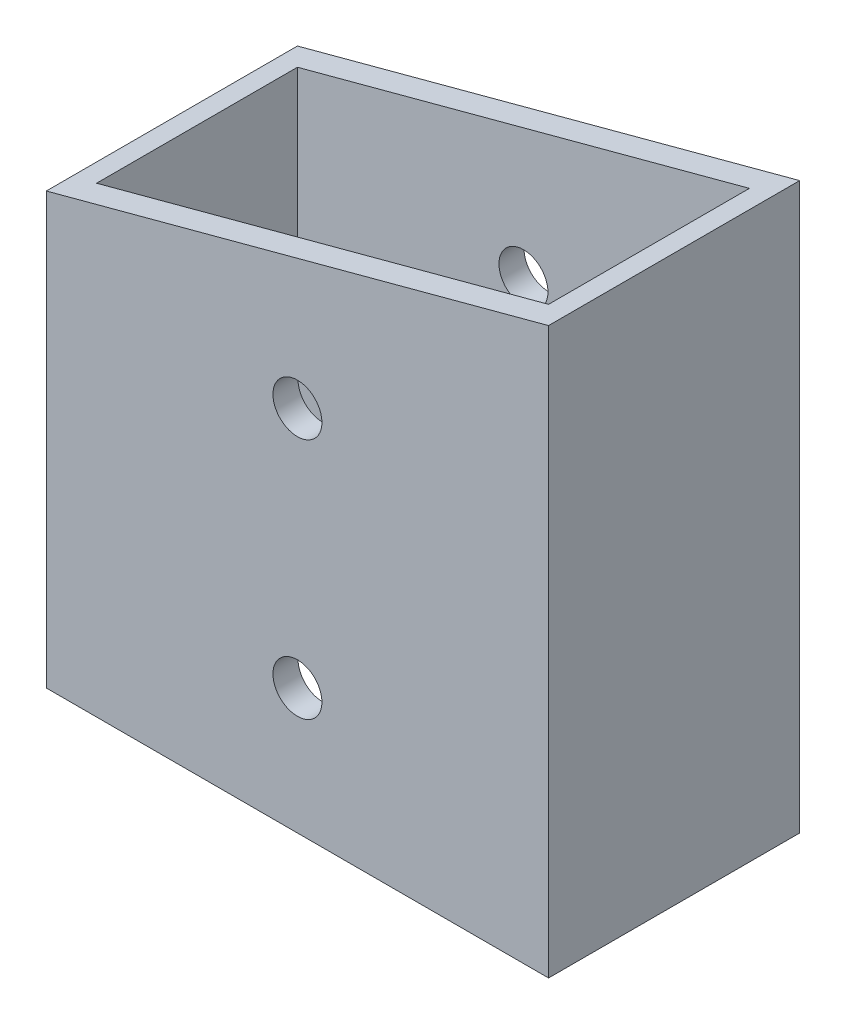
SolidWorks part; units mm, degrees
ref_plane "Front Plane" through (0, 0, 0) normal (0, 0, 1) x (1, 0, 0)
ref_plane "Top Plane" through (0, 0, 0) normal (0, 1, 0) x (1, 0, 0)
ref_plane "Right Plane" through (0, 0, 0) normal (1, 0, 0) x (0, 0, -1)
sketch "Sketch1" plane through (0, 0, 0) normal (0, 1, 0) x (1, 0, 0)
  line L1 (-25.4, -12.7) -> (25.4, -12.7)
  line L2 (-25.4, -12.7) -> (-25.4, 12.7)
  line L3 (-25.4, 12.7) -> (25.4, 12.7)
  line L4 (25.4, -12.7) -> (25.4, 12.7)
  line L5 (-25.4, -12.7) -> (25.4, 12.7) construction
  line L6 (-25.4, 12.7) -> (25.4, -12.7) construction
  point P0 (0, 0)
  dimension "D1" = 50.8
  dimension "D2" = 25.4
extrude "Extrude-Thin1" add sketch "Sketch1" along normal mid plane 107.95 thin thin type one direction reverse wall 2.54
sketch "Sketch2" plane through (0, 0, 12.7) normal (0, 0, 1) x (1, 0, 0)
  line L0 (-25.4, 53.975) -> (25.4, 53.975)
  line L1 (25.4, 53.975) -> (-25.4, 40.3632)
  line L2 (-25.4, 53.975) -> (-25.4, -53.975) construction
  line L3 (-25.4, 40.3632) -> (-25.4, 53.975)
  dimension "D1" = 15
extrude "Cut-Extrude1" cut sketch "Sketch2" against normal through all
sketch "Sketch3" plane through (0, 0, 12.7) normal (0, 0, 1) x (1, 0, 0)
  line L0 (25.4, 53.975) -> (25.4, -53.975) construction
  line L1 (-25.4, -53.975) -> (25.4, -53.975)
  line L2 (-25.4, -53.975) -> (-25.4, -3.175)
  line L3 (-25.4, -3.175) -> (25.4, -3.175)
  line L4 (25.4, -53.975) -> (25.4, -3.175)
  dimension "D1" = 50.8
extrude "Cut-Extrude2" cut sketch "Sketch3" against normal through all
sketch "Sketch4" [suppressed] plane through (0, 0, -12.7) normal (0, 0, -1) x (-1, 0, 0)
  line L2 (25.4, 40.3632) -> (-25.4, 53.975) construction
  line L3 (-25.4, -53.975) -> (25.4, -53.975) construction
  circle A0 centre (0, -41.275) radius 2.4765
  circle A1 centre (0, 34.0211) radius 2.4765
  dimension "D1" = 12.7
  dimension "D2" = 12.7
sketch "Sketch5" plane through (0, 0, -12.7) normal (0, 0, -1) x (-1, 0, 0)
  line L0 (25.4, 40.3632) -> (-25.4, 53.975) construction
  line L1 (-25.4, -3.175) -> (25.4, -3.175) construction
  circle A0 centre (0, 9.525) radius 2.4765
  circle A1 centre (0, 34.0211) radius 2.4765
  point P4 (0, 0)
  dimension "D1" = 12.7
  dimension "D2" = 12.7
extrude "Cut-Extrude3" [suppressed] cut sketch "Sketch4" against normal through all
extrude "Cut-Extrude4" cut sketch "Sketch5" against normal through all
